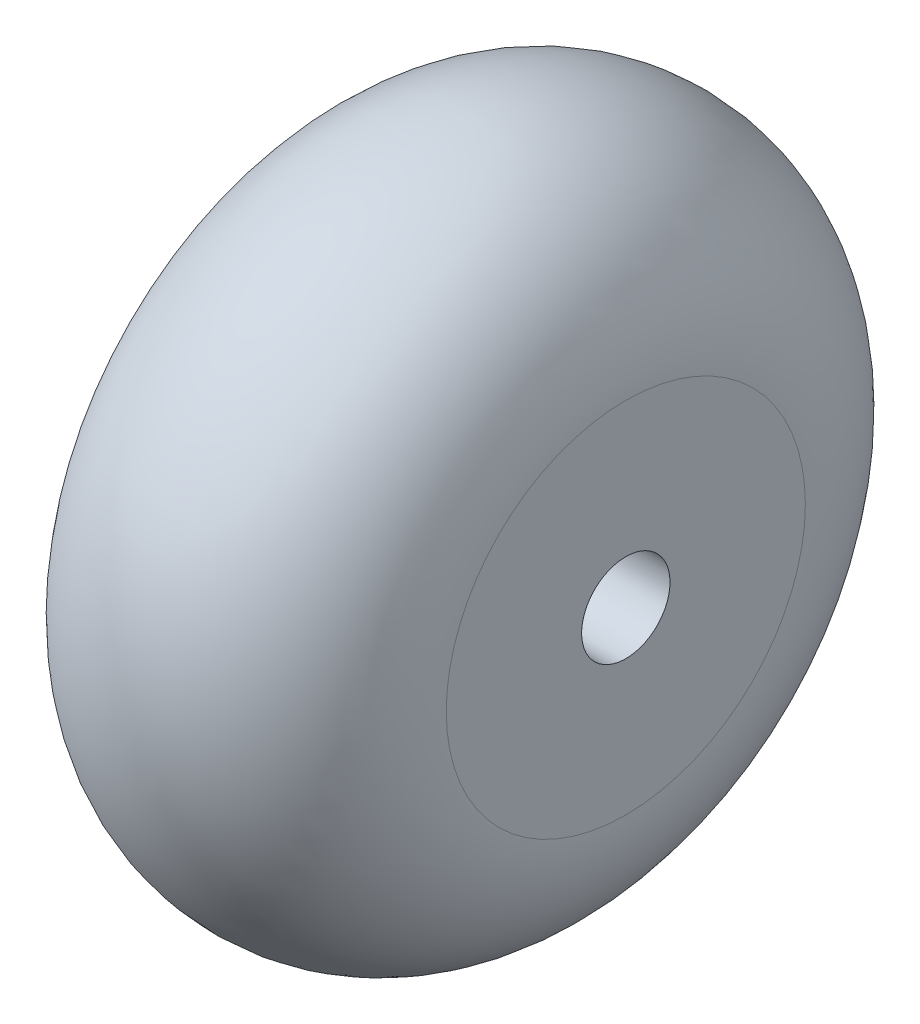
SolidWorks part; units mm, degrees
ref_plane "前视基准面" through (0, 0, 0) normal (0, 0, 1) x (1, 0, 0)
ref_plane "上视基准面" through (0, 0, 0) normal (0, 1, 0) x (1, 0, 0)
ref_plane "右视基准面" through (0, 0, 0) normal (1, 0, 0) x (0, 0, -1)
sketch "草图1" plane through (0, 0, 0) normal (0, 0, 1) x (1, 0, 0)
  line L0 (0, 73.2229) -> (0, -81.2916) construction
  line L1 (6, 6.5) -> (6, 0)
  line L2 (-6, 6.5) -> (-6, 0)
  line L3 (-23.3321, 0) -> (37.861, 0) construction
  line L4 (-6, 0) -> (6, 0)
  arc A2 (6, 6.5) -> (-6, 6.5) centre (0, 6.5) ccw
  dimension "D1" = 6
  dimension "D2" = 6.5
revolve "旋转2" add sketch "草图1" angle 360 about L4
sketch "草图2" plane through (6, 0, 0) normal (1, 0, 0) x (0, 0, -1)
  circle A0 centre (0, 0) radius 1.6
extrude "切除-拉伸1" cut sketch "草图2" against normal through all
